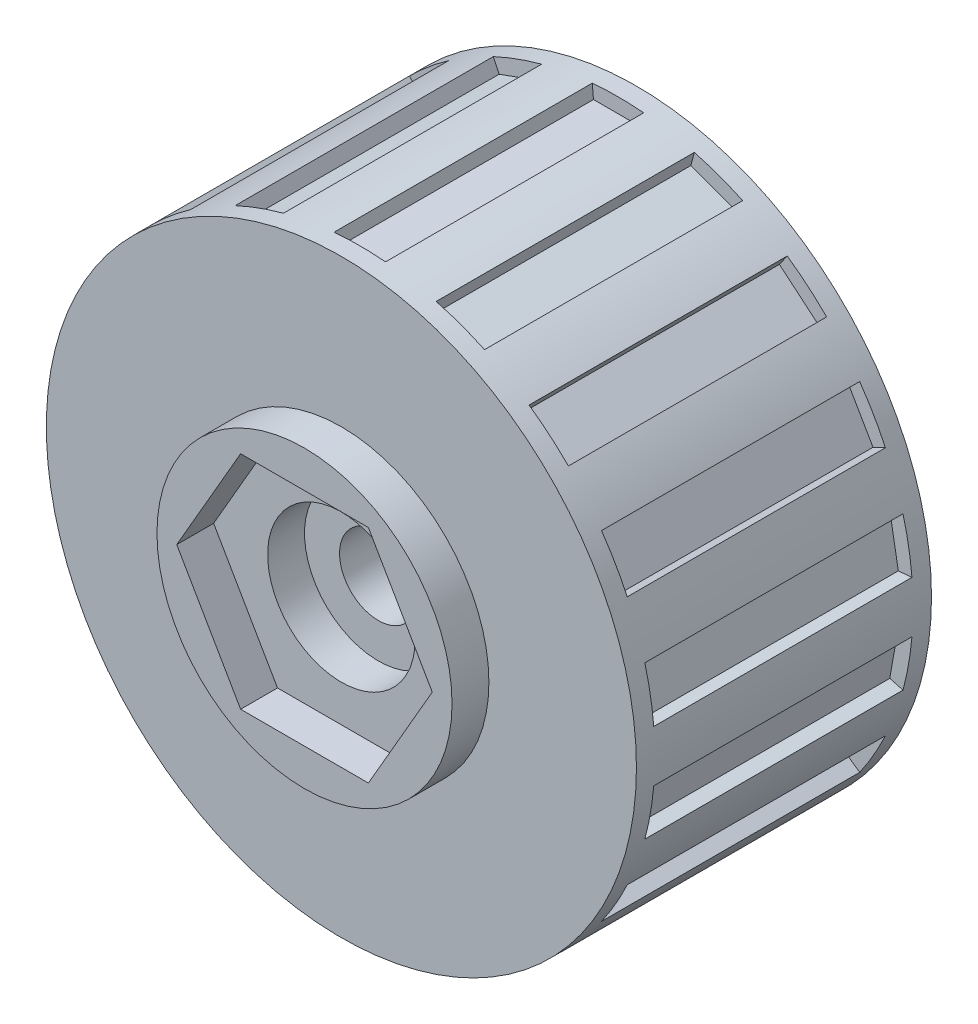
SolidWorks part; units mm, degrees
ref_plane "前视基准面" through (0, 0, 0) normal (0, 0, 1) x (1, 0, 0)
ref_plane "上视基准面" through (0, 0, 0) normal (0, 1, 0) x (1, 0, 0)
ref_plane "右视基准面" through (0, 0, 0) normal (1, 0, 0) x (0, 0, -1)
sketch "草图1" plane through (0, 0, 0) normal (0, 0, 1) x (1, 0, 0)
  circle A0 centre (0, 0) radius 80
  circle A1 centre (0, 0) radius 10.5
  dimension "D1" = 160
  dimension "D2" = 21
extrude "凸台-拉伸1" add sketch "草图1" along normal blind 80 contours A0
sketch "草图2" plane through (0, 0, 80) normal (0, 0, 1) x (1, 0, 0)
  circle A0 centre (0, 0) radius 20
  dimension "D1" = 40
extrude "切除-拉伸1" cut sketch "草图2" against normal blind 10
sketch "草图3" plane through (0, 0, 0) normal (0, 0, -1) x (-1, 0, 0)
  circle A0 centre (0, 0) radius 20
  dimension "D1" = 40
extrude "切除-拉伸2" cut sketch "草图3" against normal blind 20
ref_plane "基准面1" through (0, 0, 5) normal (0, 0, -1) x (-1, 0, 0)
sketch "草图4" plane through (0, 0, 5) normal (0, 0, -1) x (-1, 0, 0)
  line L0 (-6.6491, 76) -> (-6.9725, 79.6956)
  line L1 (6.6491, 76) -> (6.9725, 79.6956)
  line L2 (0, 80) -> (0, 0) construction
  line L3 (-6.6491, 76) -> (6.6491, 76)
  circle A0 centre (0, 0) radius 80 construction
  arc A1 (6.9725, 79.6956) -> (-6.9725, 79.6956) centre (0, 0) ccw
  dimension "D1" = 5
  dimension "D2" = 5
  dimension "D3" = 4
extrude "切除-拉伸3" cut sketch "草图4" against normal blind 70
pattern_circular "阵列(圆周)1" count 18 over 360 about axis through (0, 0, 0) along (0, 0, 1) of "切除-拉伸3"
sketch "草图6" plane through (0, 0, 0) normal (0, 0, -1) x (-1, 0, 0)
  circle A0 centre (0, 0) radius 35
  dimension "D1" = 70
extrude "切除-拉伸4" cut sketch "草图6" against normal blind 10
sketch "草图7" plane through (0, 0, 80) normal (0, 0, 1) x (1, 0, 0)
  circle A0 centre (0, 0) radius 40
  circle A1 centre (0, 0) radius 20
  dimension "D1" = 80
extrude "凸台-拉伸2" add sketch "草图7" along normal blind 10
sketch "草图8" plane through (0, 0, 90) normal (0, 0, 1) x (1, 0, 0)
  line L1 (34.641, 0) -> (17.3205, 30)
  line L2 (17.3205, 30) -> (-17.3205, 30)
  line L3 (-17.3205, 30) -> (-34.641, 0)
  line L4 (-34.641, 0) -> (-17.3205, -30)
  line L5 (-17.3205, -30) -> (17.3205, -30)
  line L6 (17.3205, -30) -> (34.641, 0)
  circle A0 centre (0, 0) radius 30 construction
  dimension "D1" = 60
extrude "切除-拉伸5" cut sketch "草图8" against normal blind 10
